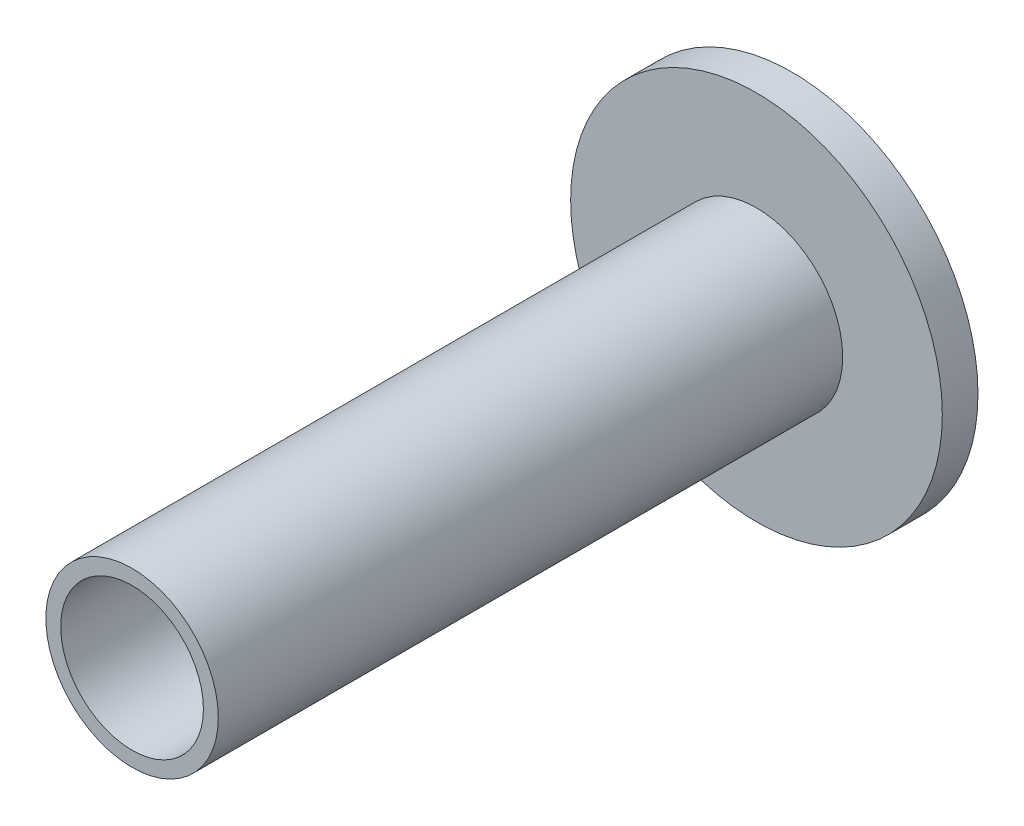
SolidWorks part; units mm, degrees
ref_plane "Front Plane" through (0, 0, 0) normal (0, 0, 1) x (1, 0, 0)
ref_plane "Top Plane" through (0, 0, 0) normal (0, 1, 0) x (1, 0, 0)
ref_plane "Right Plane" through (0, 0, 0) normal (1, 0, 0) x (0, 0, -1)
sketch "Sketch1" plane through (0, 0, 0) normal (0, 0, 1) x (1, 0, 0)
  circle A0 centre (0, 0) radius 24
  circle A1 centre (0, 0) radius 29
  dimension "D1" = 5
  dimension "D2" = 58
extrude "Boss-Extrude1" add sketch "Sketch1" along normal blind 210
sketch "Sketch2" plane through (0, 0, 0) normal (0, 0, -1) x (-1, 0, 0)
  circle A0 centre (0, 0) radius 23.7066
  circle A1 centre (0, 0) radius 62.5
extrude "Boss-Extrude2" add sketch "Sketch2" along normal blind 12
